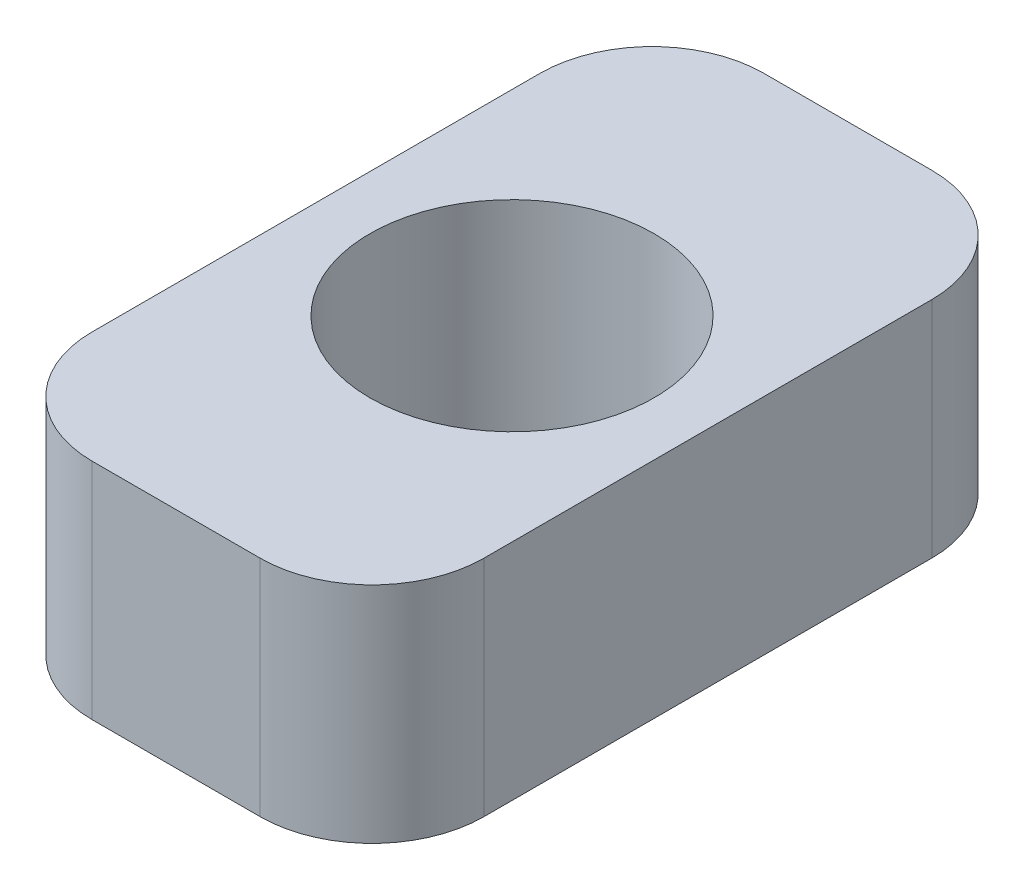
SolidWorks part; units mm, degrees
ref_plane "Front Plane" through (0, 0, 0) normal (0, 0, 1) x (1, 0, 0)
ref_plane "Top Plane" through (0, 0, 0) normal (0, 1, 0) x (1, 0, 0)
ref_plane "Right Plane" through (0, 0, 0) normal (1, 0, 0) x (0, 0, -1)
sketch "Sketch1" plane through (0, 0, 0) normal (0, 1, 0) x (1, 0, 0)
  line L1 (-17.5, -30) -> (17.5, -30)
  line L2 (-17.5, -30) -> (-17.5, 30)
  line L3 (-17.5, 30) -> (17.5, 30)
  line L4 (17.5, -30) -> (17.5, 30)
  line L5 (-17.5, -30) -> (17.5, 30) construction
  line L6 (-17.5, 30) -> (17.5, -30) construction
  circle A0 centre (0, 0) radius 12.7
  point P0 (0, 0)
  dimension "D3" = 25.4
  dimension "D1" = 35
  dimension "D2" = 60
extrude "Boss-Extrude1" add sketch "Sketch1" along normal blind 20
fillet "Fillet1" radius 10 4 edges at (17.5, 10, -30) (-17.5, 10, -30) (-17.5, 10, 30) (17.5, 10, 30)
